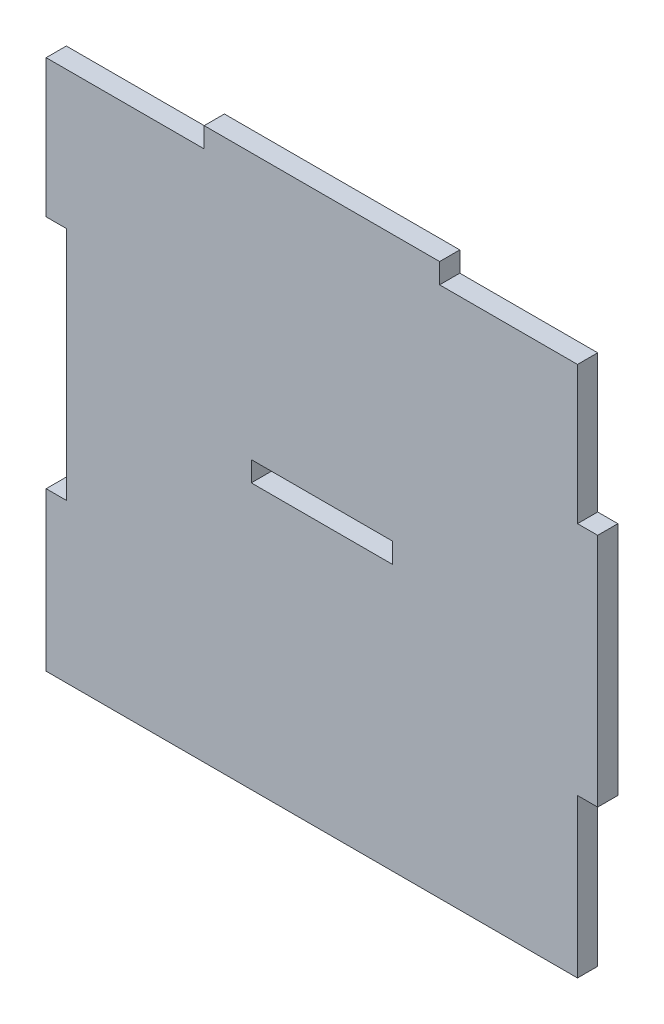
SolidWorks part; units mm, degrees
ref_plane "Front Plane" through (0, 0, 0) normal (0, 0, 1) x (1, 0, 0)
ref_plane "Top Plane" through (0, 0, 0) normal (0, 1, 0) x (1, 0, 0)
ref_plane "Right Plane" through (0, 0, 0) normal (1, 0, 0) x (0, 0, -1)
sketch "Sketch1" plane through (0, 0, 0) normal (0, 0, 1) x (1, 0, 0)
  line L0 (0, 38) -> (0, -39.5) construction
  line L5 (-38, 39.5) -> (-17.5, 39.5)
  line L6 (-38, 16) -> (-38, -16)
  line L24 (38, 39.5) -> (38, 19)
  line L26 (-41, -39.5) -> (38, -39.5)
  line L27 (-38, 0) -> (38, 0) construction
  line L28 (-17.5, 39.5) -> (-17.5, 42.5)
  line L29 (-17.5, 42.5) -> (17.5, 42.5)
  line L30 (17.5, 42.5) -> (17.5, 39.5)
  line L33 (-41, 19) -> (-41, 39.5)
  line L34 (-41, 39.5) -> (-38, 39.5)
  line L35 (-41, -19) -> (-41, -39.5)
  line L36 (38, -19) -> (38, -39.5)
  line L43 (41, 16) -> (41, -16)
  line L44 (-38, 16) -> (-38, 19)
  line L46 (17.5, 39.5) -> (38, 39.5)
  line L48 (-38, 19) -> (-41, 19)
  line L50 (-41, -19) -> (-41, -16)
  line L51 (-41, -16) -> (-38, -16)
  line L52 (38, -19) -> (38, -16)
  line L53 (38, -16) -> (41, -16)
  line L54 (41, 16) -> (41, 19)
  line L55 (41, 19) -> (38, 19)
  point P0 (0, 0)
  dimension "D1" = 79
  dimension "D2" = 76
  dimension "D3" = 3
  dimension "D4" = 35
  dimension "D5" = 3
  dimension "D6" = 76
  dimension "D7" = 35
  dimension "D8" = 3
  dimension "D9" = 3
  dimension "D10" = 3
  dimension "D11" = 3
  dimension "D12" = 35
  dimension "D13" = 0
  dimension "D14" = 20.5
extrude "Boss-Extrude1" add sketch "Sketch1" along normal blind 3
sketch "Sketch2" plane through (0, 0, 3) normal (0, 0, 1) x (1, 0, 0)
  line L0 (-41, -39.5) -> (38, -39.5) construction
  line L5 (-10.5, 3) -> (10.5, 3)
  line L6 (-10.5, 3) -> (-10.5, 0)
  line L7 (-10.5, 0) -> (10.5, 0)
  line L8 (10.5, 3) -> (10.5, 0)
  line L9 (-10.5, 3) -> (10.5, 0) construction
  line L10 (-10.5, 0) -> (10.5, 3) construction
  point P0 (0, 0)
  point P1 (0, 1.5)
  dimension "D1" = 21
  dimension "D2" = 3
  dimension "D3" = 0
  dimension "D4" = 41
extrude "Cut-Extrude1" cut sketch "Sketch2" against normal blind 3
